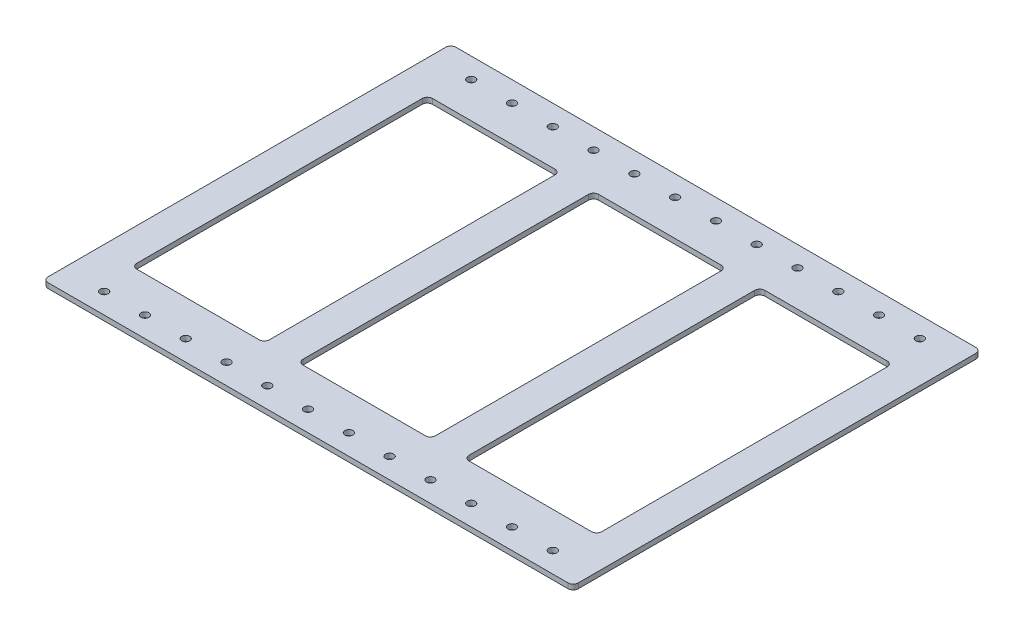
SolidWorks part; units mm, degrees
material "6061-T6 (SS)"
ref_plane "Front Plane" through (0, 0, 0) normal (0, 0, 1) x (1, 0, 0)
ref_plane "Top Plane" through (0, 0, 0) normal (0, 1, 0) x (1, 0, 0)
ref_plane "Right Plane" through (0, 0, 0) normal (1, 0, 0) x (0, 0, -1)
sketch "Sketch1" plane through (0, 0, 0) normal (0, 1, 0) x (1, 0, 0)
  line L0 (-41.275, 92.075) -> (41.275, -92.075) construction
  line L1 (165.1, -127) -> (-165.1, -127)
  line L2 (165.1, -127) -> (165.1, 127)
  line L3 (165.1, 127) -> (-165.1, 127)
  line L4 (-165.1, -127) -> (-165.1, 127)
  line L5 (165.1, -127) -> (-165.1, 127) construction
  line L6 (165.1, 127) -> (-165.1, -127) construction
  line L7 (-144.78, 92.075) -> (-62.23, 92.075)
  line L8 (-144.78, 92.075) -> (-144.78, -92.075)
  line L9 (-144.78, -92.075) -> (-62.23, -92.075)
  line L10 (-62.23, 92.075) -> (-62.23, -92.075)
  line L11 (-41.275, 92.075) -> (41.275, 92.075)
  line L12 (-41.275, 92.075) -> (-41.275, -92.075)
  line L13 (-41.275, -92.075) -> (41.275, -92.075)
  line L14 (41.275, 92.075) -> (41.275, -92.075)
  line L15 (62.23, 92.075) -> (144.78, 92.075)
  line L16 (62.23, 92.075) -> (62.23, -92.075)
  line L17 (62.23, -92.075) -> (144.78, -92.075)
  line L18 (144.78, 92.075) -> (144.78, -92.075)
  line L19 (-41.275, -92.075) -> (41.275, 92.075) construction
  point P0 (0, 0)
  dimension "D1" = 184.15
  dimension "D2" = 254
  dimension "D3" = 82.55
  dimension "D4" = 330.2
  dimension "D5" = 20.955
  dimension "D6" = 20.955
extrude "Boss-Extrude1" add sketch "Sketch1" along normal blind 3.175
fillet "Fillet1" radius 3.175 16 edges at (144.78, 1.5875, 92.075) (144.78, 1.5875, -92.075) (62.23, 1.5875, -92.075) (62.23, 1.5875, 92.075) (41.275, 1.5875, 92.075) (41.275, 1.5875, -92.075) (-41.275, 1.5875, -92.075) (-41.275, 1.5875, 92.075) (-62.23, 1.5875, 92.075) (-62.23, 1.5875, -92.075) (-144.78, 1.5875, -92.075) (-144.78, 1.5875, 92.075) (-165.1, 1.5875, -127) (165.1, 1.5875, -127) (165.1, 1.5875, 127) (-165.1, 1.5875, 127)
hole_wizard "#9 (0.196) Diameter Hole1" positions "3DSketch1" profile "Sketch2" hole size "#9" standard "ANSI Inch" end condition through all
sketch3d "3DSketch1"
  line L0 (-165.1, 3.175, 114.3) -> (165.1, 3.175, 114.3) construction
  line L1 (-165.1, 3.175, -123.825) -> (-165.1, 3.175, 123.825) construction
  line L2 (165.1, 3.175, 123.825) -> (165.1, 3.175, -123.825) construction
  line L5 (165.1, 3.175, -114.3) -> (-165.1, 3.175, -114.3) construction
  line L8 (-161.925, 3.175, 127) -> (161.925, 3.175, 127) construction
  line L9 (161.925, 3.175, -127) -> (-161.925, 3.175, -127) construction
  point P0 (-139.7, 3.175, 114.3)
  point P2 (-139.7, 3.175, -114.3)
  dimension "D1" = 12.7
  dimension "D2" = 12.7
  dimension "D3" = 25.4
sketch "Sketch2" plane through (-139.7, 3.175, 114.3) normal (1, 0, 0) x (0, 0, 1)
  line L0 (0, 0) -> (0, 3.175)
  line L1 (0, 3.175) -> (2.4892, 3.175)
  line L2 (2.4892, 3.175) -> (2.4892, 0)
  line L5 (2.4892, 0) -> (0, 0)
  line L11 (0, -6.35) -> (0, 107.95) construction
  dimension "Thru Hole Dia." = 4.9784
  dimension "Thru Hole Depth" = 3.175
pattern_linear "LPattern1" count 12 spacing 25.4 along (1, 0, 0) of "#9 (0.196) Diameter Hole1"
